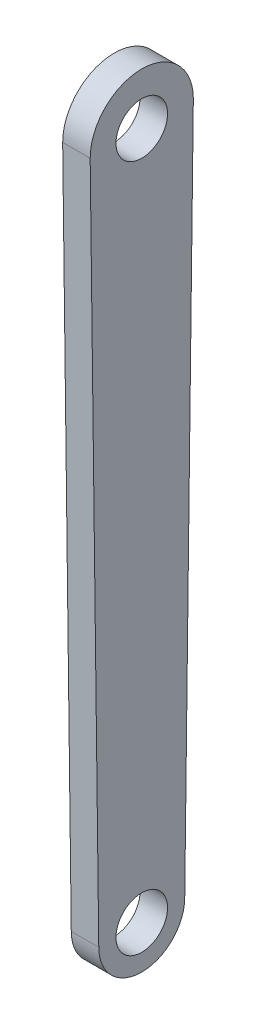
SolidWorks part; units mm, degrees
material "6061 合金"
ref_plane "前视基准面" through (0, 0, 0) normal (0, 0, 1) x (1, 0, 0)
ref_plane "上视基准面" through (0, 0, 0) normal (0, 1, 0) x (1, 0, 0)
ref_plane "右视基准面" through (0, 0, 0) normal (1, 0, 0) x (0, 0, -1)
sketch "草图1" plane through (0, 0, 0) normal (1, 0, 0) x (0, 0, -1)
  line L0 (0, 0) -> (0, -200) construction
  line L1 (15, 0) -> (12.5, -200)
  line L2 (-12.5, -200) -> (-15, 0)
  circle A0 centre (0, 0) radius 15
  circle A1 centre (0, -200) radius 12.5
  dimension "D1" = 30
  dimension "D3" = 25
  dimension "D2" = 200
extrude "凸台-拉伸1" add sketch "草图1" along normal blind 8
sketch "草图2" plane through (8, 0, 0) normal (1, 0, 0) x (0, 0, -1)
  circle A0 centre (0, 0) radius 7.5
  circle A1 centre (0, -200) radius 7.5
  dimension "D1" = 15
  dimension "D2" = 15
extrude "切除-拉伸1" cut sketch "草图2" against normal blind 10
sketch "草图3" plane through (0, 0, 0) normal (-1, 0, 0) x (0, 0, 1)
  line L0 (0, 0) -> (0, -200)
ref_plane "基准面1" through (0, 7.4412, 8.4374) normal (0, 0.6614, 0.75) x (-1, 0, 0)
